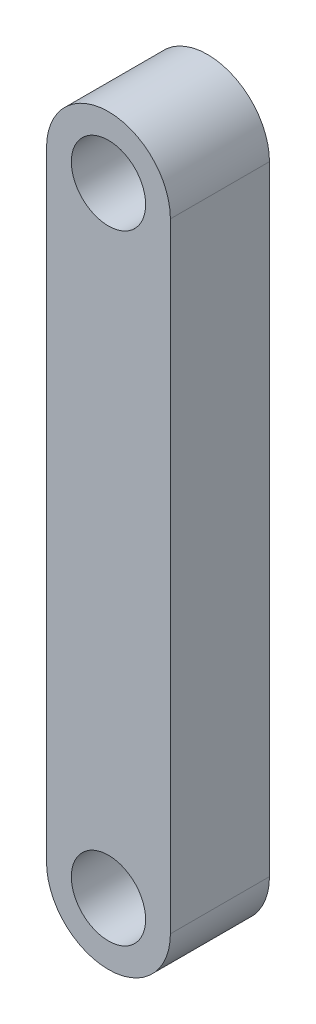
SolidWorks part; units mm, degrees
ref_plane "前视基准面" through (0, 0, 0) normal (0, 0, 1) x (1, 0, 0)
ref_plane "上视基准面" through (0, 0, 0) normal (0, 1, 0) x (1, 0, 0)
ref_plane "右视基准面" through (0, 0, 0) normal (1, 0, 0) x (0, 0, -1)
sketch "草图1" plane through (0, 0, 0) normal (0, 0, 1) x (1, 0, 0)
  line L0 (0, 0) -> (0, 27.6862) construction
  line L2 (-2.5, -12.5) -> (-2.5, 12.5)
  line L4 (2.5, -12.5) -> (2.5, 12.5)
  line L5 (0, 0) -> (26.5177, 0) construction
  arc A0 (-2.5, 12.5) -> (2.5, 12.5) centre (0, 12.5) cw
  arc A1 (-2.5, -12.5) -> (2.5, -12.5) centre (0, -12.5) ccw
  circle A2 centre (0, 12.5) radius 1.5
  circle A3 centre (0, -12.5) radius 1.5
  dimension "D1" = 2.5
  dimension "D2" = 3
  dimension "D3" = 25
extrude "凸台-拉伸1" add sketch "草图1" along normal blind 4
